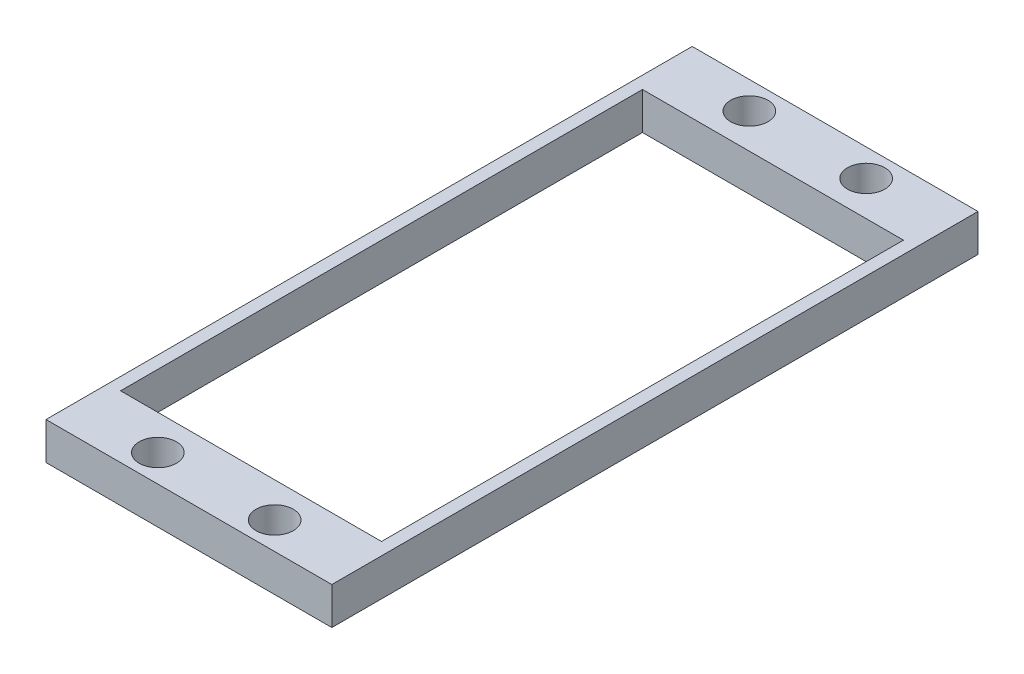
SolidWorks part; units mm, degrees
ref_plane "前基準面" through (0, 0, 0) normal (0, 0, 1) x (1, 0, 0)
ref_plane "上基準面" through (0, 0, 0) normal (0, 1, 0) x (1, 0, 0)
ref_plane "右基準面" through (0, 0, 0) normal (1, 0, 0) x (0, 0, -1)
sketch "草圖1" plane through (0, 0, 0) normal (0, 1, 0) x (1, 0, 0)
  line L0 (0, -55) -> (0, 55) construction
  line L1 (-10.5, 21) -> (10.5, 21)
  line L2 (-10.5, 21) -> (-10.5, -21)
  line L3 (-10.5, -21) -> (10.5, -21)
  line L4 (10.5, 21) -> (10.5, -21)
  line L5 (-55, 0) -> (55, 0) construction
  line L7 (11.5, 22) -> (11.5, -22)
  line L9 (-11.5, 22) -> (-11.5, -22)
  line L12 (-11.5, 22) -> (-11.5, 26)
  line L13 (-11.5, 26) -> (11.5, 26)
  line L14 (11.5, 22) -> (11.5, 26)
  line L16 (-11.5, -22) -> (-11.5, -26)
  line L17 (-11.5, -26) -> (11.5, -26)
  line L18 (11.5, -22) -> (11.5, -26)
  line L19 (-11.5, 22) -> (11.5, 22) construction
  line L22 (-11.5, -22) -> (11.5, -22) construction
  line L24 (-10.5, -21) -> (10.5, -21) construction
  circle A0 centre (-4.7, 23.8) radius 1.5
  circle A1 centre (4.7, 23.8) radius 1.5
  circle A2 centre (4.7, -23.8) radius 1.5
  circle A3 centre (-4.7, -23.8) radius 1.5
  dimension "D8" = 2.8
  dimension "D1" = 42
  dimension "D2" = 21
  dimension "D3" = 10.5
  dimension "D4" = 21
  dimension "D6" = 4
  dimension "D7" = 4
  dimension "D9" = 2.8
  dimension "D10" = 5.8
  dimension "D11" = 5.8
  dimension "D5" = 1
extrude "填料-伸長1" add sketch "草圖1" along normal blind 3
